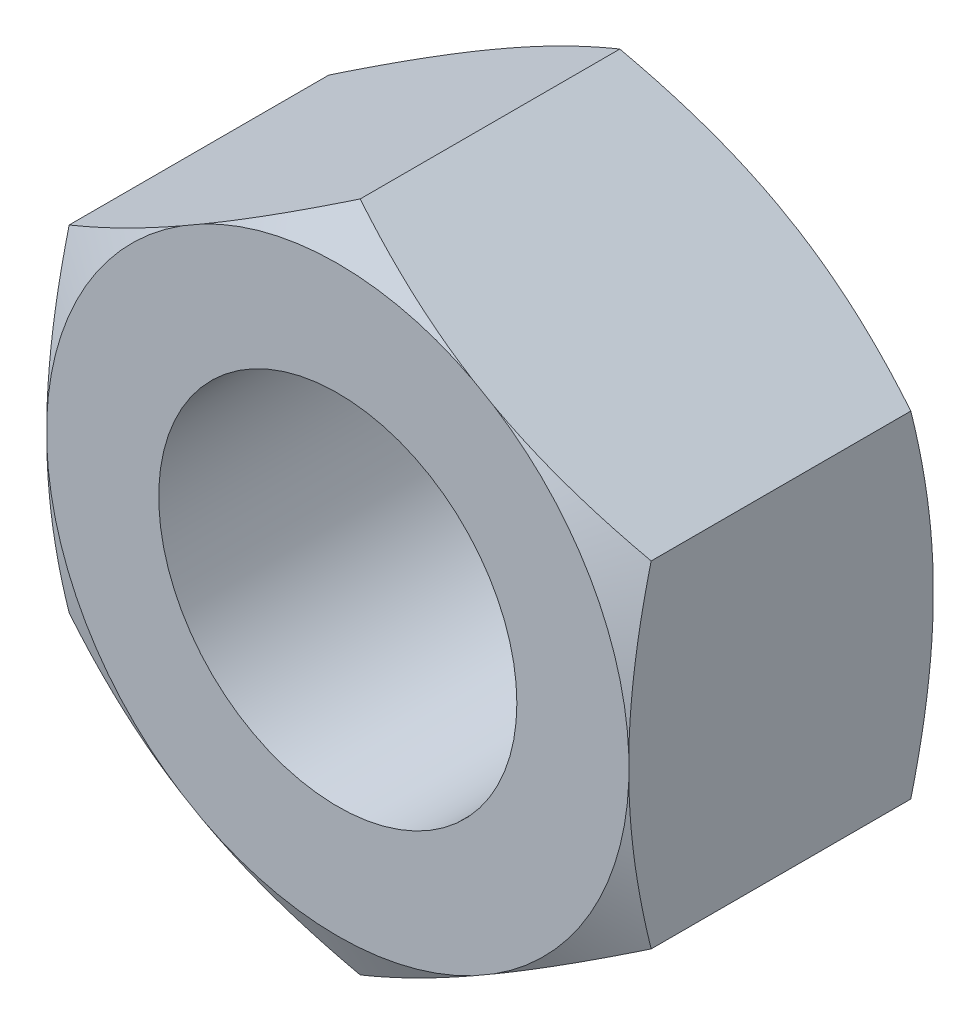
SolidWorks part; units mm, degrees
ref_plane "Front Plane" through (0, 0, 0) normal (0, 0, 1) x (1, 0, 0)
ref_plane "Top Plane" through (0, 0, 0) normal (0, 1, 0) x (1, 0, 0)
ref_plane "Right Plane" through (0, 0, 0) normal (1, 0, 0) x (0, 0, -1)
sketch "Sketch1" plane through (0, 0, 0) normal (0, 0, 1) x (1, 0, 0)
  line L1 (0, -7.5056) -> (6.5, -3.7528)
  line L2 (6.5, -3.7528) -> (6.5, 3.7528)
  line L3 (6.5, 3.7528) -> (0, 7.5056)
  line L4 (0, 7.5056) -> (-6.5, 3.7528)
  line L5 (-6.5, 3.7528) -> (-6.5, -3.7528)
  line L6 (-6.5, -3.7528) -> (0, -7.5056)
  circle A0 centre (0, 0) radius 6.5 construction
  circle A1 centre (0, 0) radius 4
  dimension "D1" = 13
extrude "Boss-Extrude1" add sketch "Sketch1" along normal blind 6.8
sketch "Sketch2" plane through (0, 0, 0) normal (1, 0, 0) x (0, 0, -1)
  line L0 (-6.8, 7.5056) -> (-6.3, 7.5056)
  line L1 (-6.8, 7.5056) -> (0, 7.5056) construction
  line L2 (-6.8, 7.5056) -> (-6.8, 6.5056)
  line L3 (-6.8, 6.5056) -> (-6.3, 7.5056)
  line L4 (-8.4332, 0) -> (2.9477, 0) construction
  line L5 (-3.4, 7.5056) -> (-3.4, 0.5628) construction
  line L6 (0, 6.5056) -> (-0.5, 7.5056)
  line L7 (0, 7.5056) -> (0, 6.5056)
  line L8 (0, 7.5056) -> (-0.5, 7.5056)
revolve "Cut-Revolve1" cut sketch "Sketch2" angle 360 about L4
